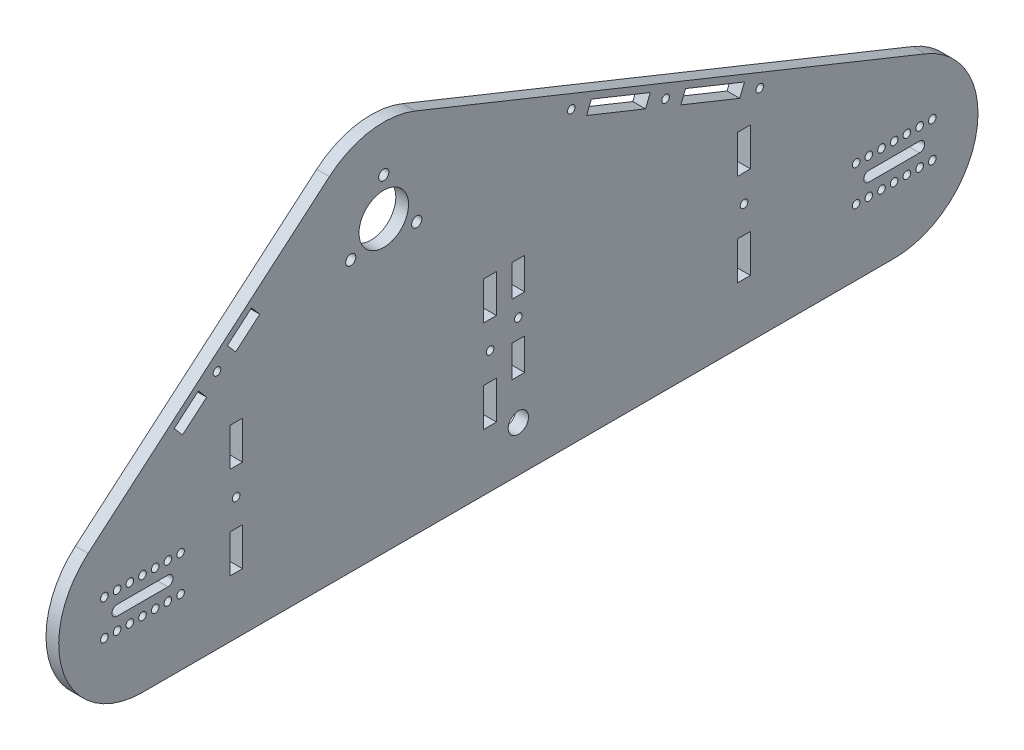
SolidWorks part; units mm, degrees
material "PMMA"
ref_plane "Piano frontale" through (0, 0, 0) normal (0, 0, 1) x (1, 0, 0)
ref_plane "Piano superiore" through (0, 0, 0) normal (0, 1, 0) x (1, 0, 0)
ref_plane "Piano destro" through (0, 0, 0) normal (1, 0, 0) x (0, 0, -1)
sketch "Model" plane through (0, 0, 0) normal (1, 0, 0) x (0, 0, -1)
  line L0 (67.9402, 99.4804) -> (217.5257, 99.4804)
  line L1 (217.5257, 99.4804) -> (217.5258, 94.516)
  line L2 (217.5258, 94.516) -> (67.9406, 94.5157)
  line L3 (67.9406, 94.5157) -> (67.9402, 99.4804)
  line L4 (75.701, 145.6492) -> (169.4508, 145.6492)
  line L5 (169.4508, 145.6492) -> (169.4508, 140.6845)
  line L6 (169.4508, 140.6845) -> (75.7013, 140.6845)
  line L7 (75.7013, 140.6845) -> (75.701, 145.6492)
  line L8 (277.8427, 54.3742) -> (278.3063, 54.3694)
  line L9 (278.3063, 54.3694) -> (7.5827, 54.3742)
  line L10 (-9.9912, 108.2246) -> (89.8382, 182.1486)
  line L11 (107.8333, 184.8972) -> (289.0756, 111.8678)
  line L12 (102.5827, 131.7594) -> (142.5827, 131.7594)
  line L13 (142.5827, 131.7594) -> (142.5827, 101.7594)
  line L14 (142.5827, 101.7594) -> (102.5827, 101.7594)
  line L15 (102.5827, 101.7594) -> (102.5827, 131.7594)
  spline S0 degree 3 poles (11.5524, 84.2317) (11.5524, 82.8135) (10.7957, 81.503) (9.5675, 80.7939) knots 0 0 0 0 1 1 1 1
  spline S1 degree 3 poles (9.5675, 80.7939) (8.3393, 80.0848) (6.8261, 80.0848) (5.5978, 80.7939) knots 0 0 0 0 1 1 1 1
  spline S2 degree 3 poles (5.5978, 80.7939) (4.3696, 81.503) (3.613, 82.8135) (3.613, 84.2317) knots 0 0 0 0 1 1 1 1
  spline S3 degree 3 poles (3.613, 84.2317) (3.613, 85.65) (4.3696, 86.9605) (5.5978, 87.6696) knots 0 0 0 0 1 1 1 1
  spline S4 degree 3 poles (5.5978, 87.6696) (6.8261, 88.3787) (8.3393, 88.3787) (9.5675, 87.6696) knots 0 0 0 0 1 1 1 1
  spline S5 degree 3 poles (9.5675, 87.6696) (10.7957, 86.9605) (11.5524, 85.65) (11.5524, 84.2317) knots 0 0 0 0 1 1 1 1
  spline S6 degree 3 poles (281.5524, 84.2317) (281.5524, 82.8135) (280.7957, 81.503) (279.5675, 80.7939) knots 0 0 0 0 1 1 1 1
  spline S7 degree 3 poles (279.5675, 80.7939) (278.3393, 80.0848) (276.826, 80.0848) (275.5978, 80.7939) knots 0 0 0 0 1 1 1 1
  spline S8 degree 3 poles (275.5978, 80.7939) (274.3696, 81.503) (273.613, 82.8135) (273.613, 84.2317) knots 0 0 0 0 1 1 1 1
  spline S9 degree 3 poles (273.613, 84.2317) (273.613, 85.65) (274.3696, 86.9605) (275.5978, 87.6696) knots 0 0 0 0 1 1 1 1
  spline S10 degree 3 poles (275.5978, 87.6696) (276.826, 88.3787) (278.3393, 88.3787) (279.5675, 87.6696) knots 0 0 0 0 1 1 1 1
  spline S11 degree 3 poles (279.5675, 87.6696) (280.7957, 86.9605) (281.5524, 85.65) (281.5524, 84.2317) knots 0 0 0 0 1 1 1 1
  spline S12 degree 3 poles (106.2634, 174.3826) (109.2777, 172.6422) (111.1346, 169.426) (111.1346, 165.9453) knots 0 0 0 0 1 1 1 1
  spline S13 degree 3 poles (111.1346, 165.9453) (111.1346, 162.4646) (109.2777, 159.2484) (106.2634, 157.508) knots 0 0 0 0 1 1 1 1
  spline S14 degree 3 poles (106.2634, 157.508) (103.249, 155.7677) (99.5352, 155.7677) (96.5208, 157.508) knots 0 0 0 0 1 1 1 1
  spline S15 degree 3 poles (96.5208, 157.508) (93.5065, 159.2484) (91.6496, 162.4646) (91.6496, 165.9453) knots 0 0 0 0 1 1 1 1
  spline S16 degree 3 poles (91.6496, 165.9453) (91.6496, 169.426) (93.5065, 172.6422) (96.5208, 174.3826) knots 0 0 0 0 1 1 1 1
  spline S17 degree 3 poles (96.5208, 174.3826) (99.5352, 176.1229) (103.249, 176.1229) (106.2634, 174.3826) knots 0 0 0 0 1 1 1 1
  spline S18 degree 3 poles (115.181, 160.1104) (115.7944, 159.7563) (116.1722, 159.1018) (116.1722, 158.3936) knots 0 0 0 0 1 1 1 1
  spline S19 degree 3 poles (116.1722, 158.3936) (116.1722, 157.6853) (115.7944, 157.0309) (115.181, 156.6768) knots 0 0 0 0 1 1 1 1
  spline S20 degree 3 poles (115.181, 156.6768) (114.5677, 156.3226) (113.812, 156.3226) (113.1986, 156.6768) knots 0 0 0 0 1 1 1 1
  spline S21 degree 3 poles (113.1986, 156.6768) (112.5852, 157.0309) (112.2074, 157.6853) (112.2074, 158.3936) knots 0 0 0 0 1 1 1 1
  spline S22 degree 3 poles (112.2074, 158.3936) (112.2074, 159.1018) (112.5852, 159.7563) (113.1986, 160.1104) knots 0 0 0 0 1 1 1 1
  spline S23 degree 3 poles (113.1986, 160.1104) (113.812, 160.4645) (114.5677, 160.4645) (115.181, 160.1104) knots 0 0 0 0 1 1 1 1
  spline S24 degree 3 poles (89.6889, 160.1104) (90.3022, 159.7563) (90.6801, 159.1018) (90.6801, 158.3936) knots 0 0 0 0 1 1 1 1
  spline S25 degree 3 poles (90.6801, 158.3936) (90.6801, 157.6853) (90.3022, 157.0309) (89.6889, 156.6768) knots 0 0 0 0 1 1 1 1
  spline S26 degree 3 poles (89.6889, 156.6768) (89.0755, 156.3226) (88.3198, 156.3226) (87.7065, 156.6768) knots 0 0 0 0 1 1 1 1
  spline S27 degree 3 poles (87.7065, 156.6768) (87.0931, 157.0309) (86.7153, 157.6853) (86.7153, 158.3936) knots 0 0 0 0 1 1 1 1
  spline S28 degree 3 poles (86.7153, 158.3936) (86.7153, 159.1018) (87.0931, 159.7563) (87.7065, 160.1104) knots 0 0 0 0 1 1 1 1
  spline S29 degree 3 poles (87.7065, 160.1104) (88.3198, 160.4645) (89.0755, 160.4645) (89.6889, 160.1104) knots 0 0 0 0 1 1 1 1
  spline S30 degree 3 poles (102.4349, 182.1873) (103.0483, 181.8331) (103.4262, 181.1787) (103.4262, 180.4704) knots 0 0 0 0 1 1 1 1
  spline S31 degree 3 poles (103.4262, 180.4704) (103.4262, 179.7622) (103.0483, 179.1077) (102.435, 178.7536) knots 0 0 0 0 1 1 1 1
  spline S32 degree 3 poles (102.435, 178.7536) (101.8216, 178.3995) (101.0659, 178.3995) (100.4525, 178.7536) knots 0 0 0 0 1 1 1 1
  spline S33 degree 3 poles (100.4525, 178.7536) (99.8392, 179.1077) (99.4613, 179.7622) (99.4613, 180.4704) knots 0 0 0 0 1 1 1 1
  spline S34 degree 3 poles (99.4613, 180.4704) (99.4613, 181.1787) (99.8392, 181.8331) (100.4525, 182.1873) knots 0 0 0 0 1 1 1 1
  spline S35 degree 3 poles (100.4525, 182.1873) (101.0659, 182.5414) (101.8216, 182.5414) (102.4349, 182.1873) knots 0 0 0 0 1 1 1 1
  spline S36 degree 3 poles (20.809, 96.941) (20.809, 97.6493) (21.1869, 98.3037) (21.8002, 98.6578) knots 0 0 0 0 1 1 1 1
  spline S37 degree 3 poles (21.8002, 98.6578) (22.4136, 99.012) (23.1693, 99.012) (23.7826, 98.6578) knots 0 0 0 0 1 1 1 1
  spline S38 degree 3 poles (23.7826, 98.6578) (24.396, 98.3037) (24.7739, 97.6493) (24.7739, 96.941) knots 0 0 0 0 1 1 1 1
  spline S39 degree 3 poles (24.7739, 96.941) (24.7739, 96.2328) (24.396, 95.5783) (23.7826, 95.2242) knots 0 0 0 0 1 1 1 1
  spline S40 degree 3 poles (23.7826, 95.2242) (23.1693, 94.8701) (22.4136, 94.8701) (21.8002, 95.2242) knots 0 0 0 0 1 1 1 1
  spline S41 degree 3 poles (21.8002, 95.2242) (21.1869, 95.5783) (20.809, 96.2328) (20.809, 96.941) knots 0 0 0 0 1 1 1 1
  spline S42 degree 3 poles (260.4931, 96.9408) (260.4931, 97.6491) (260.8709, 98.3035) (261.4843, 98.6577) knots 0 0 0 0 1 1 1 1
  spline S43 degree 3 poles (261.4843, 98.6577) (262.0976, 99.0118) (262.8533, 99.0118) (263.4667, 98.6577) knots 0 0 0 0 1 1 1 1
  spline S44 degree 3 poles (263.4667, 98.6577) (264.0801, 98.3035) (264.4579, 97.6491) (264.4579, 96.9408) knots 0 0 0 0 1 1 1 1
  spline S45 degree 3 poles (264.4579, 96.9408) (264.4579, 96.2326) (264.0801, 95.5781) (263.4667, 95.224) knots 0 0 0 0 1 1 1 1
  spline S46 degree 3 poles (263.4667, 95.224) (262.8533, 94.8699) (262.0976, 94.8699) (261.4843, 95.224) knots 0 0 0 0 1 1 1 1
  spline S47 degree 3 poles (261.4843, 95.224) (260.8709, 95.5781) (260.4931, 96.2326) (260.4931, 96.9408) knots 0 0 0 0 1 1 1 1
  spline S48 degree 3 poles (68.2691, 143.1669) (68.2691, 143.8751) (68.6469, 144.5296) (69.2603, 144.8837) knots 0 0 0 0 1 1 1 1
  spline S49 degree 3 poles (69.2603, 144.8837) (69.8737, 145.2378) (70.6294, 145.2378) (71.2427, 144.8837) knots 0 0 0 0 1 1 1 1
  spline S50 degree 3 poles (71.2427, 144.8837) (71.8561, 144.5296) (72.2339, 143.8751) (72.2339, 143.1669) knots 0 0 0 0 1 1 1 1
  spline S51 degree 3 poles (72.2339, 143.1669) (72.2339, 142.4586) (71.8561, 141.8042) (71.2427, 141.45) knots 0 0 0 0 1 1 1 1
  spline S52 degree 3 poles (71.2427, 141.45) (70.6294, 141.0959) (69.8737, 141.0959) (69.2603, 141.45) knots 0 0 0 0 1 1 1 1
  spline S53 degree 3 poles (69.2603, 141.45) (68.6469, 141.8042) (68.2691, 142.4586) (68.2691, 143.1669) knots 0 0 0 0 1 1 1 1
  spline S54 degree 3 poles (172.9986, 143.1669) (172.9986, 143.8751) (173.3764, 144.5296) (173.9898, 144.8837) knots 0 0 0 0 1 1 1 1
  spline S55 degree 3 poles (173.9898, 144.8837) (174.6032, 145.2378) (175.3589, 145.2378) (175.9722, 144.8837) knots 0 0 0 0 1 1 1 1
  spline S56 degree 3 poles (175.9722, 144.8837) (176.5856, 144.5296) (176.9634, 143.8751) (176.9634, 143.1669) knots 0 0 0 0 1 1 1 1
  spline S57 degree 3 poles (176.9634, 143.1669) (176.9634, 142.4586) (176.5856, 141.8042) (175.9722, 141.45) knots 0 0 0 0 1 1 1 1
  spline S58 degree 3 poles (175.9722, 141.45) (175.3589, 141.0959) (174.6032, 141.0959) (173.9898, 141.45) knots 0 0 0 0 1 1 1 1
  spline S59 degree 3 poles (173.9898, 141.45) (173.3764, 141.8042) (172.9986, 142.4586) (172.9986, 143.1669) knots 0 0 0 0 1 1 1 1
  spline S60 degree 3 poles (85.7246, 137.2262) (85.7246, 137.9345) (86.1025, 138.5889) (86.7159, 138.943) knots 0 0 0 0 1 1 1 1
  spline S61 degree 3 poles (86.7159, 138.943) (87.3292, 139.2972) (88.0849, 139.2972) (88.6983, 138.943) knots 0 0 0 0 1 1 1 1
  spline S62 degree 3 poles (88.6983, 138.943) (89.3116, 138.5889) (89.6895, 137.9345) (89.6895, 137.2262) knots 0 0 0 0 1 1 1 1
  spline S63 degree 3 poles (89.6895, 137.2262) (89.6895, 136.518) (89.3116, 135.8635) (88.6983, 135.5094) knots 0 0 0 0 1 1 1 1
  spline S64 degree 3 poles (88.6983, 135.5094) (88.0849, 135.1553) (87.3292, 135.1553) (86.7159, 135.5094) knots 0 0 0 0 1 1 1 1
  spline S65 degree 3 poles (86.7159, 135.5094) (86.1025, 135.8635) (85.7246, 136.518) (85.7246, 137.2262) knots 0 0 0 0 1 1 1 1
  spline S66 degree 3 poles (148.3215, 137.2262) (148.3215, 137.9345) (148.6994, 138.5889) (149.3127, 138.943) knots 0 0 0 0 1 1 1 1
  spline S67 degree 3 poles (149.3127, 138.943) (149.9261, 139.2972) (150.6818, 139.2972) (151.2952, 138.943) knots 0 0 0 0 1 1 1 1
  spline S68 degree 3 poles (151.2952, 138.943) (151.9085, 138.5889) (152.2864, 137.9345) (152.2864, 137.2262) knots 0 0 0 0 1 1 1 1
  spline S69 degree 3 poles (152.2864, 137.2262) (152.2864, 136.518) (151.9085, 135.8635) (151.2952, 135.5094) knots 0 0 0 0 1 1 1 1
  spline S70 degree 3 poles (151.2952, 135.5094) (150.6818, 135.1553) (149.9261, 135.1553) (149.3127, 135.5094) knots 0 0 0 0 1 1 1 1
  spline S71 degree 3 poles (149.3127, 135.5094) (148.6994, 135.8635) (148.3215, 136.518) (148.3215, 137.2262) knots 0 0 0 0 1 1 1 1
  spline S72 degree 3 poles (218.5454, 91.2336) (218.5454, 91.9418) (218.9232, 92.5963) (219.5366, 92.9504) knots 0 0 0 0 1 1 1 1
  spline S73 degree 3 poles (219.5366, 92.9504) (220.15, 93.3045) (220.9057, 93.3045) (221.519, 92.9504) knots 0 0 0 0 1 1 1 1
  spline S74 degree 3 poles (221.519, 92.9504) (222.1324, 92.5963) (222.5102, 91.9418) (222.5102, 91.2336) knots 0 0 0 0 1 1 1 1
  spline S75 degree 3 poles (222.5102, 91.2336) (222.5102, 90.5253) (222.1324, 89.8709) (221.519, 89.5168) knots 0 0 0 0 1 1 1 1
  spline S76 degree 3 poles (221.519, 89.5168) (220.9057, 89.1626) (220.15, 89.1626) (219.5366, 89.5168) knots 0 0 0 0 1 1 1 1
  spline S77 degree 3 poles (219.5366, 89.5168) (218.9232, 89.8709) (218.5454, 90.5253) (218.5454, 91.2336) knots 0 0 0 0 1 1 1 1
  spline S78 degree 3 poles (62.9042, 91.2341) (62.9042, 91.9423) (63.282, 92.5968) (63.8954, 92.9509) knots 0 0 0 0 1 1 1 1
  spline S79 degree 3 poles (63.8954, 92.9509) (64.5088, 93.305) (65.2645, 93.305) (65.8778, 92.9509) knots 0 0 0 0 1 1 1 1
  spline S80 degree 3 poles (65.8778, 92.9509) (66.4912, 92.5968) (66.869, 91.9423) (66.869, 91.2341) knots 0 0 0 0 1 1 1 1
  spline S81 degree 3 poles (66.869, 91.2341) (66.869, 90.5258) (66.4912, 89.8714) (65.8778, 89.5173) knots 0 0 0 0 1 1 1 1
  spline S82 degree 3 poles (65.8778, 89.5173) (65.2645, 89.1631) (64.5088, 89.1631) (63.8954, 89.5173) knots 0 0 0 0 1 1 1 1
  spline S83 degree 3 poles (63.8954, 89.5173) (63.282, 89.8714) (62.9042, 90.5258) (62.9042, 91.2341) knots 0 0 0 0 1 1 1 1
  spline S84 degree 3 poles (169.3736, 91.2336) (169.3736, 91.9418) (169.7514, 92.5963) (170.3648, 92.9504) knots 0 0 0 0 1 1 1 1
  spline S85 degree 3 poles (170.3648, 92.9504) (170.9781, 93.3045) (171.7338, 93.3045) (172.3472, 92.9504) knots 0 0 0 0 1 1 1 1
  spline S86 degree 3 poles (172.3472, 92.9504) (172.9605, 92.5963) (173.3384, 91.9418) (173.3384, 91.2336) knots 0 0 0 0 1 1 1 1
  spline S87 degree 3 poles (173.3384, 91.2336) (173.3384, 90.5253) (172.9605, 89.8709) (172.3472, 89.5168) knots 0 0 0 0 1 1 1 1
  spline S88 degree 3 poles (172.3472, 89.5168) (171.7338, 89.1626) (170.9781, 89.1626) (170.3648, 89.5168) knots 0 0 0 0 1 1 1 1
  spline S89 degree 3 poles (170.3648, 89.5168) (169.7514, 89.8709) (169.3736, 90.5253) (169.3736, 91.2336) knots 0 0 0 0 1 1 1 1
  spline S90 degree 3 poles (112.2515, 91.2336) (112.2515, 91.9418) (112.6293, 92.5963) (113.2427, 92.9504) knots 0 0 0 0 1 1 1 1
  spline S91 degree 3 poles (113.2427, 92.9504) (113.8561, 93.3045) (114.6118, 93.3045) (115.2251, 92.9504) knots 0 0 0 0 1 1 1 1
  spline S92 degree 3 poles (115.2251, 92.9504) (115.8385, 92.5963) (116.2163, 91.9418) (116.2163, 91.2336) knots 0 0 0 0 1 1 1 1
  spline S93 degree 3 poles (116.2163, 91.2336) (116.2163, 90.5253) (115.8385, 89.8709) (115.2251, 89.5168) knots 0 0 0 0 1 1 1 1
  spline S94 degree 3 poles (115.2251, 89.5168) (114.6118, 89.1626) (113.8561, 89.1626) (113.2427, 89.5168) knots 0 0 0 0 1 1 1 1
  spline S95 degree 3 poles (113.2427, 89.5168) (112.6293, 89.8709) (112.2515, 90.5253) (112.2515, 91.2336) knots 0 0 0 0 1 1 1 1
  spline S96 degree 3 poles (289.0756, 111.8678) (292.9178, 110.2369) (296.1347, 108.0507) (298.8362, 105.3491) knots 0 0 0 0 1 1 1 1
  spline S97 degree 3 poles (298.8362, 105.3491) (301.5378, 102.6475) (303.7241, 99.4306) (305.235, 95.8585) knots 0 0 0 0 1 1 1 1
  spline S98 degree 3 poles (305.235, 95.8585) (306.7459, 92.2864) (307.5813, 88.3591) (307.5813, 84.2367) knots 0 0 0 0 1 1 1 1
  spline S99 degree 3 poles (307.5813, 84.2367) (307.5813, 67.7468) (294.2137, 54.3791) (277.8427, 54.3742) knots 0 0 0 0 1 1 1 1
  spline S100 degree 3 poles (7.5827, 54.3742) (-8.766, 54.3791) (-22.1337, 67.7468) (-22.1337, 84.2367) knots 0 0 0 0 1 1 1 1
  spline S101 degree 3 poles (-22.1337, 84.2367) (-22.1337, 92.4816) (-18.7918, 99.946) (-13.3886, 105.3491) knots 0 0 0 0 1 1 1 1
  spline S102 degree 3 poles (-13.3886, 105.3491) (-12.0378, 106.6999) (-10.5582, 107.9219) (-9.9912, 108.2246) knots 0 0 0 0 1 1 1 1
  spline S103 degree 3 poles (89.8382, 182.1486) (90.5198, 182.6635) (91.6227, 183.3375) (92.7755, 183.8987) knots 0 0 0 0 1 1 1 1
  spline S104 degree 3 poles (92.7755, 183.8987) (93.9282, 184.4598) (95.1308, 184.9082) (96.3649, 185.2389) knots 0 0 0 0 1 1 1 1
  spline S105 degree 3 poles (96.3649, 185.2389) (97.5989, 185.5696) (98.8646, 185.7825) (100.1435, 185.8729) knots 0 0 0 0 1 1 1 1
  spline S106 degree 3 poles (100.1435, 185.8729) (101.4224, 185.9633) (102.7145, 185.9311) (104.0017, 185.7714) knots 0 0 0 0 1 1 1 1
  spline S107 degree 3 poles (104.0017, 185.7714) (105.2888, 185.6116) (106.5709, 185.3244) (107.8333, 184.8972) knots 0 0 0 0 1 1 1 1
sketch "Schizzo5" plane through (0, 0, 0) normal (1, 0, 0) x (0, 0, -1)
  line L0 (-95, 0) -> (201, 0) construction
  line L1 (0, 81) -> (0, 0) construction
  dimension "D1" = 95
  dimension "D2" = 201
  dimension "D3" = 81
sketch "Schizzo2" plane through (0, 0, 0) normal (1, 0, 0) x (0, 0, -1)
  line L0 (0, 81) -> (-42.1808, 56.6469) construction
  line L1 (0, 81) -> (0, 129.7062) construction
  line L2 (0, 81) -> (42.1808, 56.6469) construction
  line L4 (0, 81) -> (0, 0) construction
  circle A0 centre (-95, 0) radius 2
  circle A1 centre (201, 0) radius 2
  circle A2 centre (12.9904, 73.5) radius 2
  circle A3 centre (-12.9904, 73.5) radius 2
  circle A4 centre (0, 96) radius 2
  circle A5 centre (0, 81) radius 15 construction
  circle A6 centre (0, 81) radius 9.75
  circle A7 centre (0, 81) radius 20.25 construction
  circle A8 centre (0, 81) radius 17.5 construction
  point P15 (0, 96)
  point P16 (12.9904, 73.5)
  point P17 (-12.9904, 73.5)
  dimension "D1" = 4
  dimension "D3" = 4
  dimension "D4" = 30
  dimension "D7" = 19.5
  dimension "D10" = 40.5
  dimension "D11" = 35
  dimension "D5" = 120
  dimension "D6" = 120
sketch "Schizzo3" plane through (0, 0, 0) normal (1, 0, 0) x (0, 0, -1)
  line L0 (-95, 0) -> (-95, -14.8819) construction
  line L1 (201, 0) -> (201, -14.8819) construction
  line L2 (-95, -33) -> (201, -33)
  line L3 (-116.4107, 25.1114) -> (-21.4107, 106.1114)
  line L4 (12.3346, 111.6081) -> (213.3346, 30.6081)
  line L5 (-88.7024, 88.8238) -> (-49.1191, 42.3989) construction
  line L6 (124.2365, 99.4016) -> (101.4328, 42.8146) construction
  line L7 (53, 95.2206) -> (53, -33) construction
  line L9 (184.7962, 36.718) -> (37.1353, 96.2231) construction
  line L21 (19.8748, 94.143) -> (22.8748, 89.143) construction
  arc A0 (12.3346, 111.6081) -> (-21.4107, 106.1114) centre (0, 81) ccw
  arc A1 (-116.4107, 25.1114) -> (-95, -33) centre (-95, 0) ccw
  arc A2 (213.3346, 30.6081) -> (201, -33) centre (201, 0) cw
  circle A3 centre (-95, 0) radius 47.625 construction
  circle A4 centre (201, 0) radius 47.625 construction
  circle A5 centre (0, 81) radius 47.625 construction
  circle A11 centre (-65.6667, 61.8066) radius 1.5
  circle A12 centre (110.9657, 66.4705) radius 1.5
  circle A13 centre (73.865, 81.4216) radius 1.5
  circle A14 centre (148.0665, 51.5195) radius 1.5
  point P19 (-68.9107, 65.6114)
  point P22 (112.8346, 71.1081)
  point P32 (53, -33)
  point P44 (110.9657, 66.4705)
  dimension "D2" = 33
  dimension "D3" = 95.25
  dimension "D4" = 95.25
  dimension "D7" = 40.452
  dimension "D11" = 5
  dimension "D12" = 40
  dimension "D8" = 21.949
  dimension "D13" = 40
  dimension "D20" = 5
extrude "Estrusione-Estrusione1" add sketch "Schizzo3" along normal blind 5
extrude "Taglio-Estrusione1" cut sketch "Schizzo2" along normal through all
sketch "Schizzo4" plane through (0, 0, 0) normal (1, 0, 0) x (0, 0, -1)
  line L5 (53, -2.6867) -> (53, -128.4682) construction
  line L11 (53, 95.2206) -> (53, -33) construction
  line L24 (73.865, 81.4216) -> (110.9657, 66.4705) construction
  line L29 (80.8214, 78.6183) -> (104.0093, 69.2739) construction
  line L30 (104.9438, 71.5926) -> (103.0749, 66.9551)
  line L31 (103.0749, 66.9551) -> (79.8869, 76.2995)
  line L32 (81.7558, 80.9371) -> (79.8869, 76.2995)
  line L33 (104.9438, 71.5926) -> (81.7558, 80.9371)
  line L34 (101.4328, 42.8146) -> (119.4142, 87.4352) construction
  line L35 (124.2365, 99.4016) -> (101.4328, 42.8146) construction
  line L36 (118.8566, 65.986) -> (116.9877, 61.3484)
  line L37 (116.9877, 61.3484) -> (140.1757, 52.004)
  line L38 (142.0445, 56.6416) -> (140.1757, 52.004)
  line L39 (118.8566, 65.986) -> (142.0445, 56.6416)
  line L40 (-82.5077, 50.7328) -> (-72.9958, 58.8429)
  line L41 (-72.9958, 58.8429) -> (-69.7518, 55.0382)
  line L42 (-69.7518, 55.0382) -> (-79.2637, 46.928)
  line L43 (-79.2637, 46.928) -> (-82.5077, 50.7328)
  line L44 (-49.1191, 42.3989) -> (-88.7024, 88.8238) construction
  line L45 (-116.4107, 25.1114) -> (-21.4107, 106.1114) construction
  line L46 (-80.8857, 48.8304) -> (-50.4477, 74.7828) construction
  line L47 (-61.5816, 68.5751) -> (-58.3375, 64.7703)
  line L48 (-52.0697, 76.6852) -> (-61.5816, 68.5751)
  line L49 (-48.8257, 72.8804) -> (-52.0697, 76.6852)
  line L50 (-58.3375, 64.7703) -> (-48.8257, 72.8804)
  circle A0 centre (0, 81) radius 32.5 construction
  point P51 (92.4154, 73.9461)
  point P64 (-80.8857, 48.8304)
  point P71 (-65.6667, 61.8066)
  dimension "D14" = 25
  dimension "D15" = 5
  dimension "D16" = 12.5
  dimension "D17" = 5
  dimension "D18" = 40
extrude "Taglio-Estrusione2" cut sketch "Schizzo4" along normal through all
sketch "Schizzo6" plane through (5, 0, 0) normal (1, 0, 0) x (0, 0, -1)
  line L0 (-95, -33) -> (201, -33) construction
  line L1 (44.37, 4.5) -> (39.37, 4.5)
  line L2 (44.37, 4.5) -> (44.37, -10.5)
  line L3 (44.37, -10.5) -> (39.37, -10.5)
  line L4 (39.37, 4.5) -> (39.37, -10.5)
  line L6 (44.37, 40.84) -> (44.37, 25.84)
  line L7 (44.37, 25.84) -> (39.37, 25.84)
  line L8 (39.37, 40.84) -> (39.37, 25.84)
  line L9 (44.37, 40.84) -> (39.37, 40.84)
  line L10 (139.37, 40.84) -> (139.37, 25.84)
  line L11 (144.37, 25.84) -> (139.37, 25.84)
  line L12 (144.37, 40.84) -> (144.37, 25.84)
  line L13 (144.37, 40.84) -> (139.37, 40.84)
  line L14 (139.37, 4.5) -> (139.37, -10.5)
  line L15 (144.37, -10.5) -> (139.37, -10.5)
  line L16 (144.37, 4.5) -> (144.37, -10.5)
  line L17 (144.37, 4.5) -> (139.37, 4.5)
  line L18 (-60.63, 4.5) -> (-60.63, -10.5)
  line L19 (-55.63, -10.5) -> (-60.63, -10.5)
  line L20 (-55.63, 4.5) -> (-55.63, -10.5)
  line L21 (-55.63, 4.5) -> (-60.63, 4.5)
  line L22 (-60.63, 40.84) -> (-60.63, 25.84)
  line L23 (-55.63, 25.84) -> (-60.63, 25.84)
  line L24 (-55.63, 40.84) -> (-55.63, 25.84)
  line L25 (-55.63, 40.84) -> (-60.63, 40.84)
  line L26 (-95, -33) -> (201, -33) construction
  line L27 (53, -33) -> (53, 73.4295) construction
  line L28 (41.87, 25.84) -> (41.87, 4.5) construction
  line L38 (57.4149, 20.84) -> (48.5851, 20.84) construction
  line L39 (50.5, 40.84) -> (55.5, 40.84)
  line L40 (50.5, 40.84) -> (50.5, 28.34)
  line L41 (50.5, 28.34) -> (55.5, 28.34)
  line L42 (55.5, 40.84) -> (55.5, 28.34)
  line L43 (50.5, 0.84) -> (55.5, 0.84)
  line L44 (50.5, 0.84) -> (50.5, 13.34)
  line L45 (50.5, 13.34) -> (55.5, 13.34)
  line L46 (55.5, 0.84) -> (55.5, 13.34)
  line L47 (53, 28.34) -> (53, 13.34) construction
  circle A0 centre (41.87, 15.17) radius 1.5
  circle A1 centre (-58.13, 15.17) radius 1.5
  circle A2 centre (141.87, 15.17) radius 1.5
  circle A3 centre (53, -15) radius 4
  circle A4 centre (53, 20.84) radius 1.5
  point P60 (53, 20.84)
  dimension "D15" = 5
  dimension "D16" = 12.5
  dimension "D18" = 40
  dimension "D7" = 3
  dimension "D10" = 8
  dimension "D17" = 3
  dimension "D1" = 22.5
  dimension "D2" = 5
  dimension "D3" = 15
  dimension "D9" = 11.13
  dimension "D11" = 18
  dimension "D12" = 21.34
  dimension "D13" = 35.84
  dimension "D4" = 2
  dimension "D5" = 2
  dimension "D6" = 2
  dimension "D8" = 2
extrude "Taglio-Estrusione3" cut sketch "Schizzo6" along direction (1, 0, 0) on the side against the normal through all
sketch "Schizzo7" plane through (0, 0, 0) normal (1, 0, 0) x (0, 0, -1)
  line L0 (-105, 0) -> (-85, 0) construction
  line L1 (-105, 2) -> (-85, 2)
  line L2 (-105, -2) -> (-85, -2)
  line L3 (191, 0) -> (211, 0) construction
  line L4 (191, 2) -> (211, 2)
  line L5 (191, -2) -> (211, -2)
  line L6 (-95.8595, 7) -> (49904.1405, 7) construction
  line L7 (-107.9229, 6.9974) -> (49892.0771, 6.9974) construction
  line L8 (-95, 0) -> (-95, 7) construction
  line L9 (-56.257, -7) -> (-50056.257, -7) construction
  line L10 (53, -29.7252) -> (53, 29.7252) construction
  line L11 (-95, 0) -> (201, 0) construction
  arc A0 (-105, 2) -> (-105, -2) centre (-105, 0) ccw
  arc A1 (-85, -2) -> (-85, 2) centre (-85, 0) ccw
  arc A2 (191, 2) -> (191, -2) centre (191, 0) ccw
  arc A3 (211, -2) -> (211, 2) centre (211, 0) ccw
  circle A4 centre (-95, 7) radius 1.5
  circle A5 centre (-90, 7) radius 1.5
  circle A6 centre (-85, 7) radius 1.5
  circle A7 centre (-80, 7) radius 1.5
  circle A10 centre (-100, 7) radius 1.5
  circle A11 centre (-105, 7) radius 1.5
  circle A12 centre (-110, 7) radius 1.5
  circle A17 centre (-80, -7) radius 1.5
  circle A18 centre (-85, -7) radius 1.5
  circle A19 centre (-90, -7) radius 1.5
  circle A20 centre (-95, -7) radius 1.5
  circle A21 centre (-100, -7) radius 1.5
  circle A22 centre (-105, -7) radius 1.5
  circle A23 centre (-110, -7) radius 1.5
  circle A28 centre (216, -7) radius 1.5
  circle A29 centre (211, -7) radius 1.5
  circle A30 centre (206, -7) radius 1.5
  circle A31 centre (201, -7) radius 1.5
  circle A32 centre (196, -7) radius 1.5
  circle A33 centre (191, -7) radius 1.5
  circle A34 centre (186, -7) radius 1.5
  circle A39 centre (186, 7) radius 1.5
  circle A40 centre (191, 7) radius 1.5
  circle A41 centre (196, 7) radius 1.5
  circle A42 centre (201, 7) radius 1.5
  circle A43 centre (206, 7) radius 1.5
  circle A44 centre (211, 7) radius 1.5
  circle A45 centre (216, 7) radius 1.5
  point P2 (-95, 0)
  point P11 (201, 0)
  point P30 (53, 0)
  point P31 (53, 0)
  dimension "D2" = 2
  dimension "D4" = 2
  dimension "D7" = 3
  dimension "D1" = 10
  dimension "D3" = 10
  dimension "D5" = 7
  dimension "D6" = 7
  dimension "D8" = 4
  dimension "D9" = 4
extrude "Taglio-Estrusione4" cut sketch "Schizzo7" along direction (1, 0, 0) on the side of the normal through all
equation "\"Thickness\"=5"
equation "\"D1@Estrusione-Estrusione1\"=\"Thickness\""
equation "\"D17@Schizzo4\"=\"Thickness\""
equation "\"D15@Schizzo4\"=\"Thickness\""
equation "\"D2@Schizzo6\"=\"Thickness\""
equation "\"D15@Schizzo6\"=\"Thickness\""
